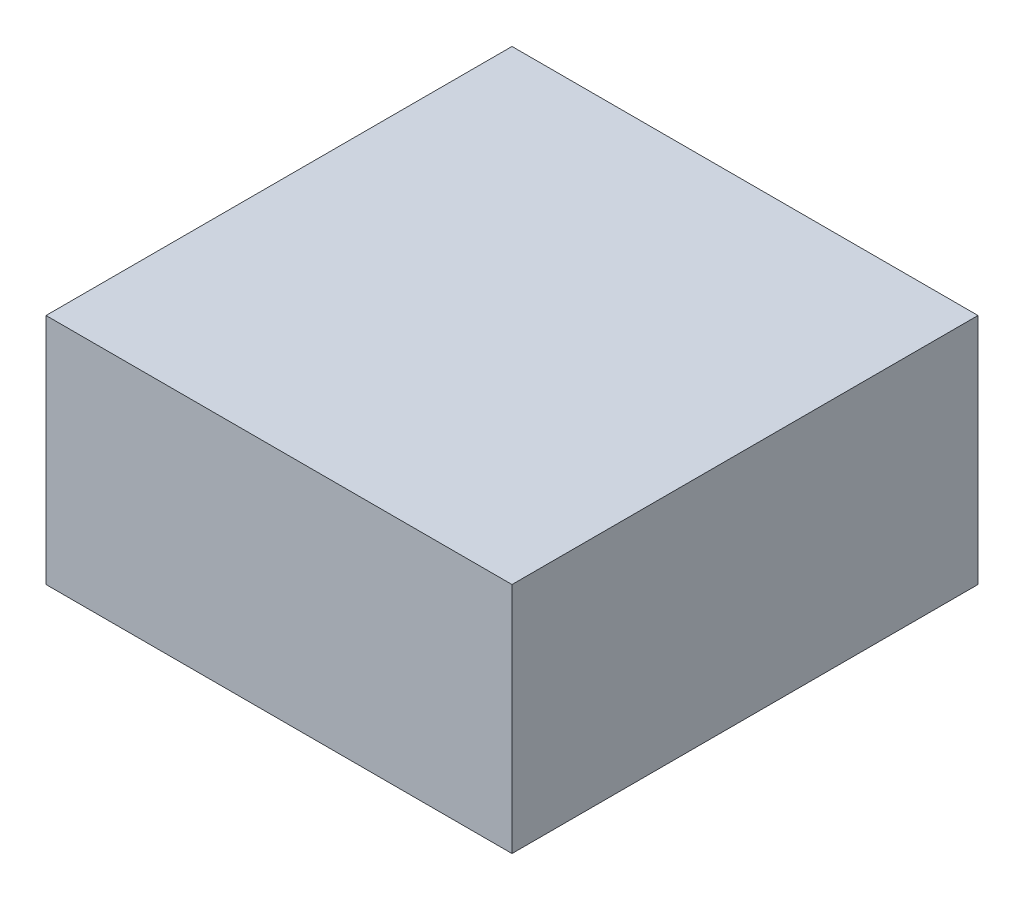
SolidWorks part; units mm, degrees
ref_plane "Alzado" through (0, 0, 0) normal (0, 0, 1) x (1, 0, 0)
ref_plane "Planta" through (0, 0, 0) normal (0, 1, 0) x (1, 0, 0)
ref_plane "Vista lateral" through (0, 0, 0) normal (1, 0, 0) x (0, 0, -1)
sketch "Croquis1" plane through (0, 0, 0) normal (0, 1, 0) x (1, 0, 0)
  line L1 (0, 0) -> (400, 0)
  line L2 (0, 0) -> (0, 400)
  line L3 (0, 400) -> (400, 400)
  line L4 (400, 0) -> (400, 400)
  dimension "D1" = 400
  dimension "D2" = 400
extrude "Saliente-Extruir1" add sketch "Croquis1" along normal blind 200
